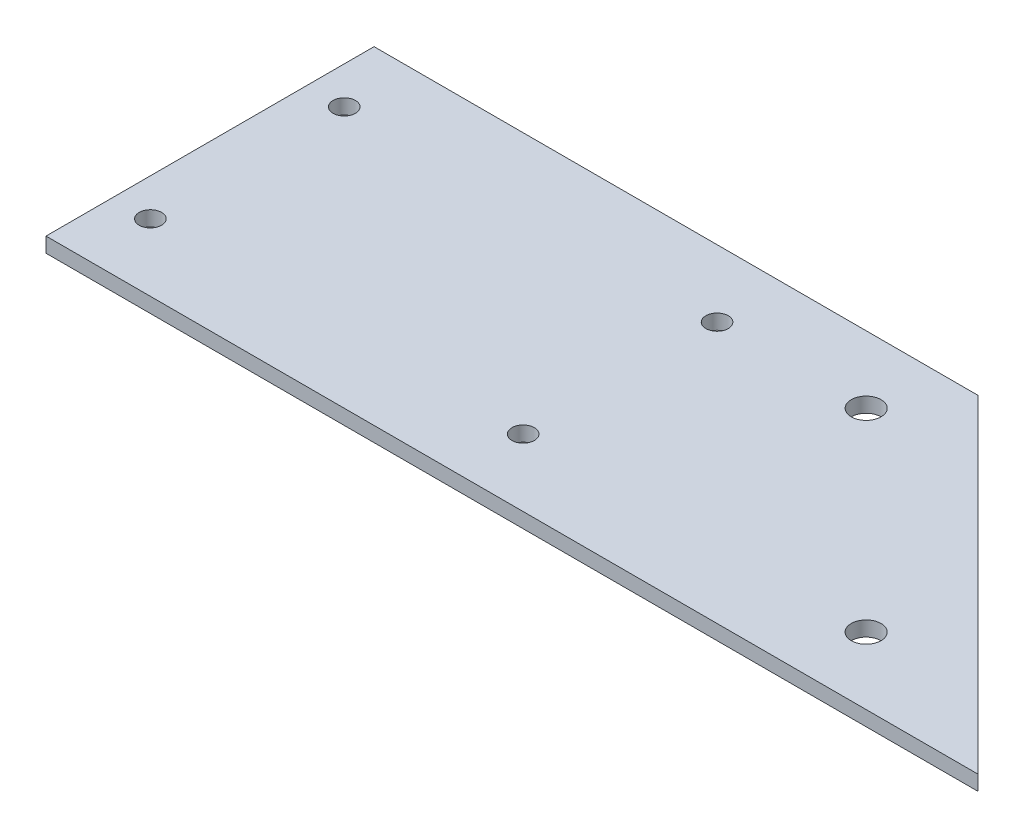
SolidWorks part; units mm, degrees
ref_plane "Front Plane" through (0, 0, 0) normal (0, 0, 1) x (1, 0, 0)
ref_plane "Top Plane" through (0, 0, 0) normal (0, 1, 0) x (1, 0, 0)
ref_plane "Right Plane" through (0, 0, 0) normal (1, 0, 0) x (0, 0, -1)
sketch "Sketch1" plane through (0, 0, 0) normal (0, 1, 0) x (1, 0, 0)
  line L0 (81, 44) -> (125, 0)
  line L1 (0, 0) -> (125, 0)
  line L2 (0, 0) -> (0, 44)
  line L3 (0, 44) -> (81, 44)
  circle A0 centre (5, 35) radius 1.5
  circle A1 centre (5, 9) radius 1.5
  circle A2 centre (55, 9) radius 1.5
  circle A3 centre (55, 35) radius 1.5
  circle A4 centre (75, 35) radius 2
  circle A5 centre (101, 9) radius 2
  dimension "D7" = 46
  dimension "D8" = 4
  dimension "D11" = 3
  dimension "D12" = 3
  dimension "D13" = 3
  dimension "D14" = 3
  dimension "D1" = 50
  dimension "D2" = 26
  dimension "D3" = 44
  dimension "D4" = 26
  dimension "D5" = 9
  dimension "D6" = 135
  dimension "D9" = 20
  dimension "D10" = 125
  dimension "D15" = 9
  dimension "D16" = 5
extrude "Boss-Extrude1" add sketch "Sketch1" along normal blind 2
